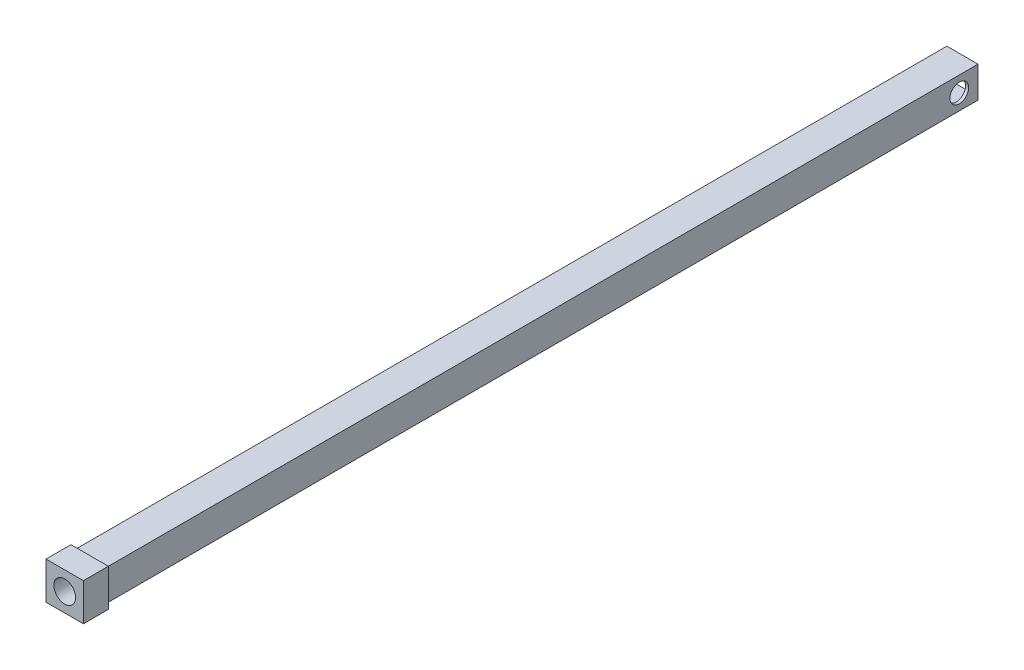
SolidWorks part; units mm, degrees
ref_plane "Plan de face" through (0, 0, 0) normal (0, 0, 1) x (1, 0, 0)
ref_plane "Plan de dessus" through (0, 0, 0) normal (0, 1, 0) x (1, 0, 0)
ref_plane "Plan de droite" through (0, 0, 0) normal (1, 0, 0) x (0, 0, -1)
sketch "Esquisse2" plane through (0, 0, 0) normal (0, 0, 1) x (1, 0, 0)
  line L1 (-5, -5) -> (5, -5)
  line L2 (-5, -5) -> (-5, 5)
  line L3 (-5, 5) -> (5, 5)
  line L4 (5, -5) -> (5, 5)
  line L5 (-5, -5) -> (5, 5) construction
  line L6 (-5, 5) -> (5, -5) construction
  line L7 (4, -4) -> (-4, -4)
  line L8 (4, -4) -> (4, 4)
  line L9 (4, 4) -> (-4, 4)
  line L10 (-4, -4) -> (-4, 4)
  line L11 (4, -4) -> (-4, 4) construction
  line L12 (4, 4) -> (-4, -4) construction
  point P0 (0, 0)
  dimension "D3" = 8
  dimension "D1" = 10
  dimension "D2" = 10
  dimension "D4" = 8
extrude "Boss.-Extru.1" add sketch "Esquisse2" along normal blind 280
sketch "Esquisse3" plane through (5, 0, 0) normal (1, 0, 0) x (0, 0, -1)
  line L1 (-280, 5) -> (0, 5) construction
  circle A1 centre (-6, 0) radius 3
  dimension "D4" = 6
  dimension "D5" = 6
  dimension "D6" = 5
extrude "Enlèv. mat.-Extru.1" cut sketch "Esquisse3" against normal blind 52
sketch "Esquisse4" plane through (0, 0, 280) normal (0, 0, 1) x (1, 0, 0)
  line L1 (-6, -6) -> (6, -6)
  line L2 (-6, -6) -> (-6, 6)
  line L3 (-6, 6) -> (6, 6)
  line L4 (6, -6) -> (6, 6)
  line L5 (-6, -6) -> (6, 6) construction
  line L6 (-6, 6) -> (6, -6) construction
  circle A0 centre (0, 0) radius 3.5
  point P0 (0, 0)
  dimension "D3" = 7
  dimension "D1" = 12
  dimension "D2" = 12
extrude "Boss.-Extru.2" add sketch "Esquisse4" along normal blind 8
